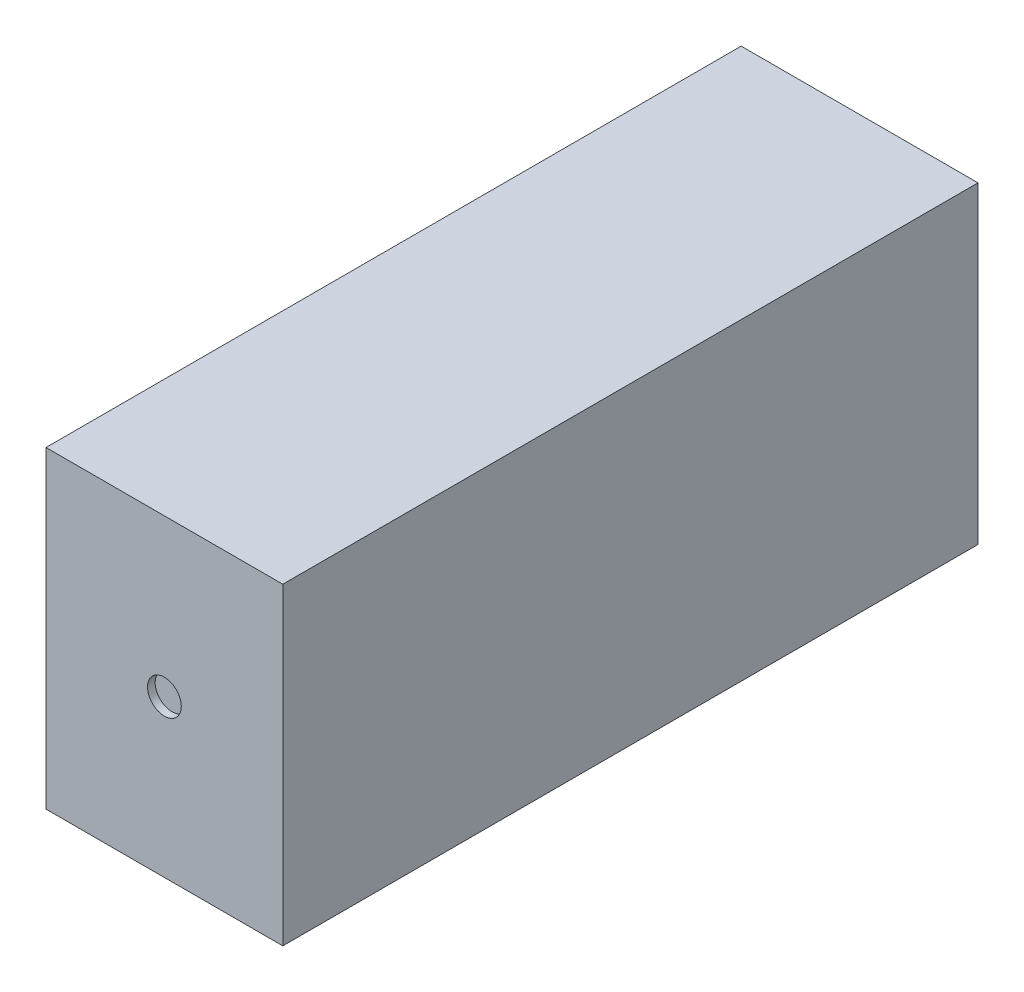
SolidWorks part; units mm, degrees
ref_plane "Front Plane" through (0, 0, 0) normal (0, 0, 1) x (1, 0, 0)
ref_plane "Top Plane" through (0, 0, 0) normal (0, 1, 0) x (1, 0, 0)
ref_plane "Right Plane" through (0, 0, 0) normal (1, 0, 0) x (0, 0, -1)
sketch "Sketch1" plane through (0, 0, 0) normal (0, 0, 1) x (1, 0, 0)
  line L1 (0, 0) -> (78.74, 0)
  line L2 (0, 0) -> (0, 104.14)
  line L3 (0, 104.14) -> (78.74, 104.14)
  line L4 (78.74, 0) -> (78.74, 104.14)
extrude "Boss-Extrude1" add sketch "Sketch1" along normal blind 231.14
sketch "Sketch2" plane through (0, 0, 231.14) normal (0, 0, 1) x (1, 0, 0)
  circle A0 centre (39.37, 52.07) radius 5.6142
extrude "Cut-Extrude1" cut sketch "Sketch2" against normal blind 2.54
